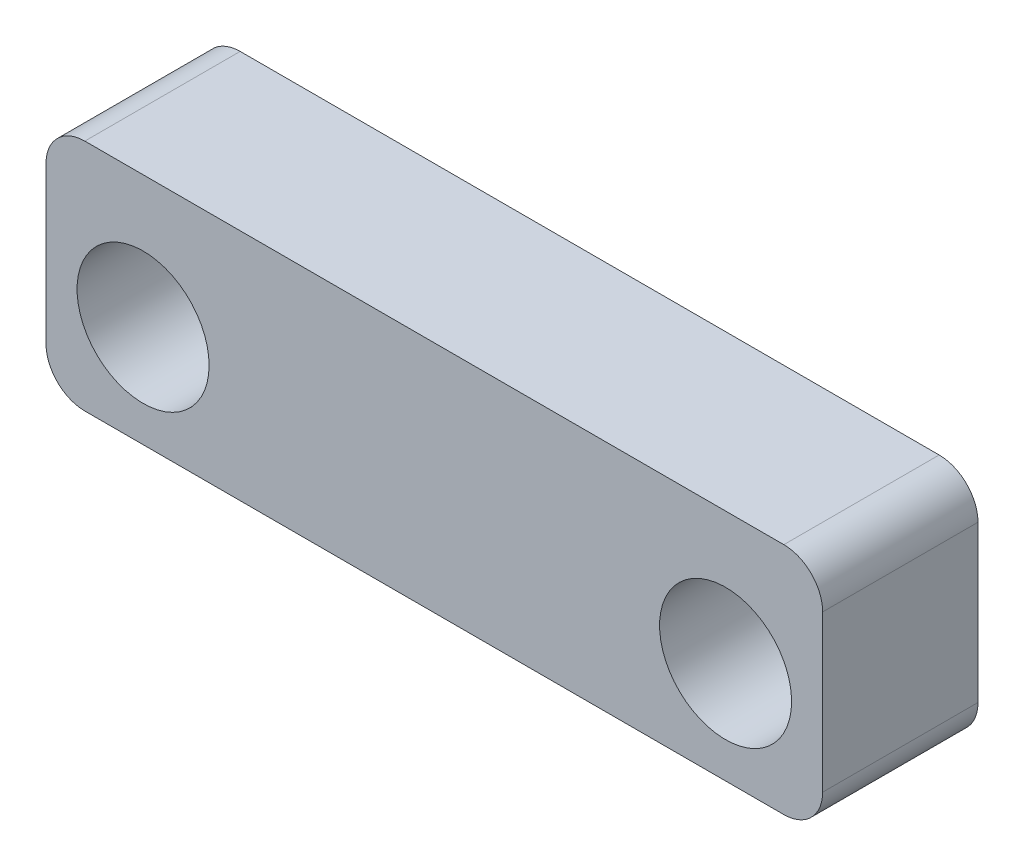
SolidWorks part; units mm, degrees
ref_plane "Plano frontal" through (0, 0, 0) normal (0, 0, 1) x (1, 0, 0)
ref_plane "Plano superior" through (0, 0, 0) normal (0, 1, 0) x (1, 0, 0)
ref_plane "Plano direito" through (0, 0, 0) normal (1, 0, 0) x (0, 0, -1)
ref_plane "Plane1" through (0, 0, 133.3657) normal (0, 0, 1) x (1, 0, 0)
sketch "Sketch2" plane through (0, 0, 133.3657) normal (0, 0, 1) x (1, 0, 0)
  line L1 (-31.3276, 41.1785) -> (-11.3276, 41.1785)
  line L2 (-31.3276, 41.1785) -> (-31.3276, 35.1582)
  line L3 (-31.3276, 35.1582) -> (-11.3276, 35.1582)
  line L4 (-11.3276, 41.1785) -> (-11.3276, 35.1582)
extrude "Boss-Extrude1" add sketch "Sketch2" along normal blind 4
fillet "Fillet1" radius 1 4 edges at (-11.3276, 35.1582, 135.3657) (-11.3276, 41.1785, 135.3657) (-31.3276, 35.1582, 135.3657) (-31.3276, 41.1785, 135.3657)
hole_wizard "M3 Clearance Hole1" positions "Sketch5" profile "Sketch3" hole size "M3" standard "ISO"
sketch "Sketch5" plane through (0, 0, 137.3657) normal (0, 0, 1) x (1, 0, 0)
  point P0 (-28.8276, 37.7785)
  point P2 (-13.8276, 37.7785)
sketch "Sketch3" plane through (-28.8276, 37.7785, 137.3657) normal (1, 0, 0) x (0, -1, 0)
  line L0 (0, 0) -> (0, 17.5215)
  line L1 (0, 17.5215) -> (1.7, 16.5)
  line L2 (1.7, 16.5) -> (1.7, 0)
  line L5 (1.7, 0) -> (0, 0)
  line L10 (0, 17.5215) -> (-1.7, 16.5) construction
  line L11 (0, -6.35) -> (0, 107.95) construction
  dimension "Hole Dia." = 3.4
  dimension "Hole Depth" = 16.5
  dimension "Drill Angle" = 118
